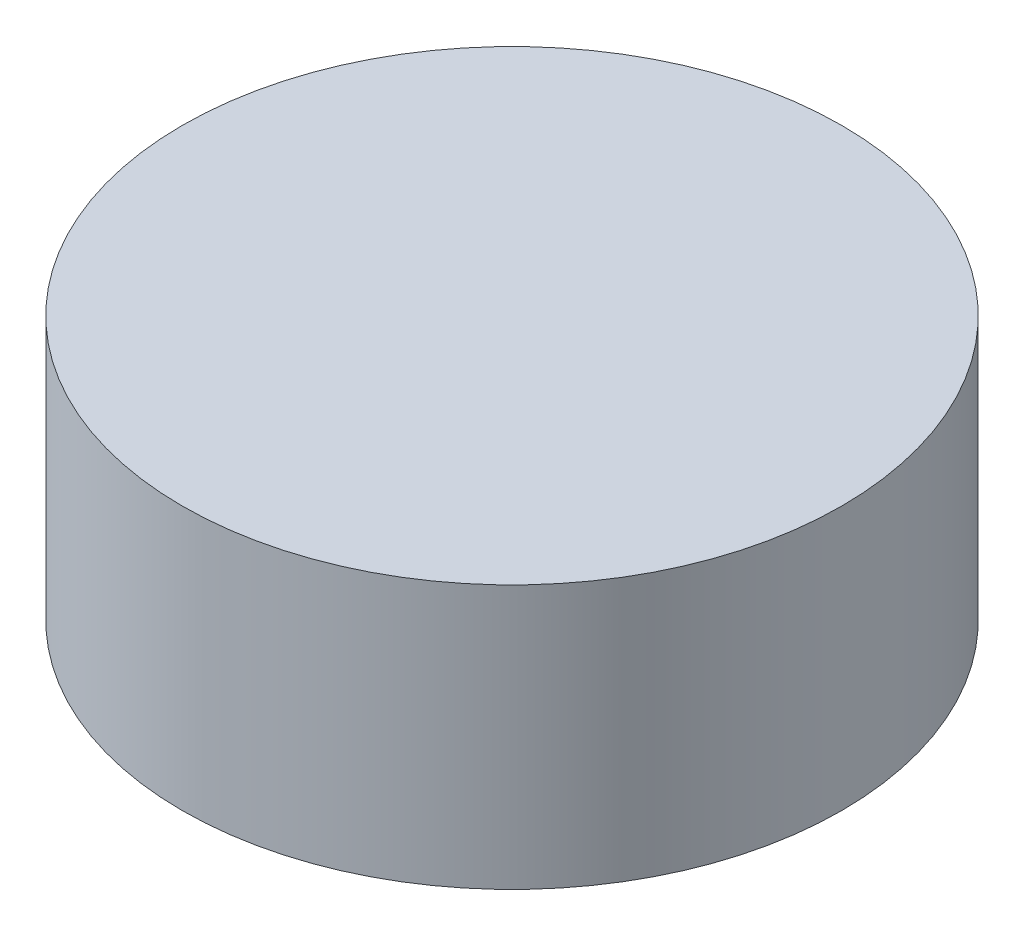
SolidWorks part; units mm, degrees
ref_plane "Plan de face" through (0, 0, 0) normal (0, 0, 1) x (1, 0, 0)
ref_plane "Plan de dessus" through (0, 0, 0) normal (0, 1, 0) x (1, 0, 0)
ref_plane "Plan de droite" through (0, 0, 0) normal (1, 0, 0) x (0, 0, -1)
sketch "Esquisse1" plane through (0, 0, 0) normal (0, 1, 0) x (1, 0, 0)
  circle A0 centre (0, 0) radius 25
  dimension "D1" = 50
extrude "Boss.-Extru.1" add sketch "Esquisse1" along normal mid plane 20
